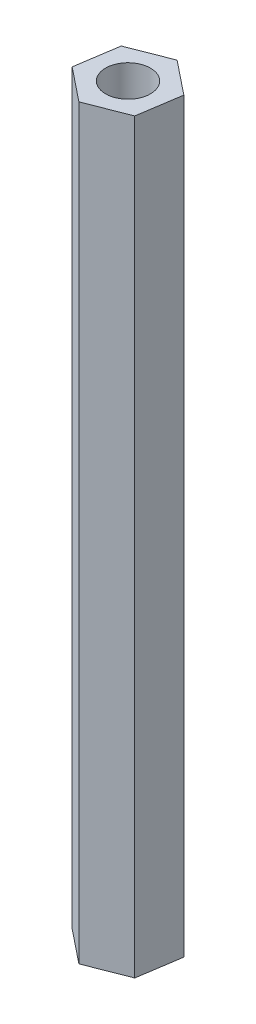
SolidWorks part; units mm, degrees
ref_plane "Front Plane" through (0, 0, 0) normal (0, 0, 1) x (1, 0, 0)
ref_plane "Top Plane" through (0, 0, 0) normal (0, 1, 0) x (1, 0, 0)
ref_plane "Right Plane" through (0, 0, 0) normal (1, 0, 0) x (0, 0, -1)
sketch "Sketch1" plane through (0, 0, 0) normal (0, 1, 0) x (1, 0, 0)
  line L1 (2.2542, -1.8033) -> (2.6888, 1.0505)
  line L2 (2.6888, 1.0505) -> (0.4347, 2.8538)
  line L3 (0.4347, 2.8538) -> (-2.2542, 1.8033)
  line L4 (-2.2542, 1.8033) -> (-2.6888, -1.0505)
  line L5 (-2.6888, -1.0505) -> (-0.4347, -2.8538)
  line L6 (-0.4347, -2.8538) -> (2.2542, -1.8033)
  circle A0 centre (0, 0) radius 1.5
  circle A1 centre (0, 0) radius 2.5 construction
  dimension "D1" = 3
  dimension "D2" = 5
extrude "Boss-Extrude1" add sketch "Sketch1" along normal blind 50
